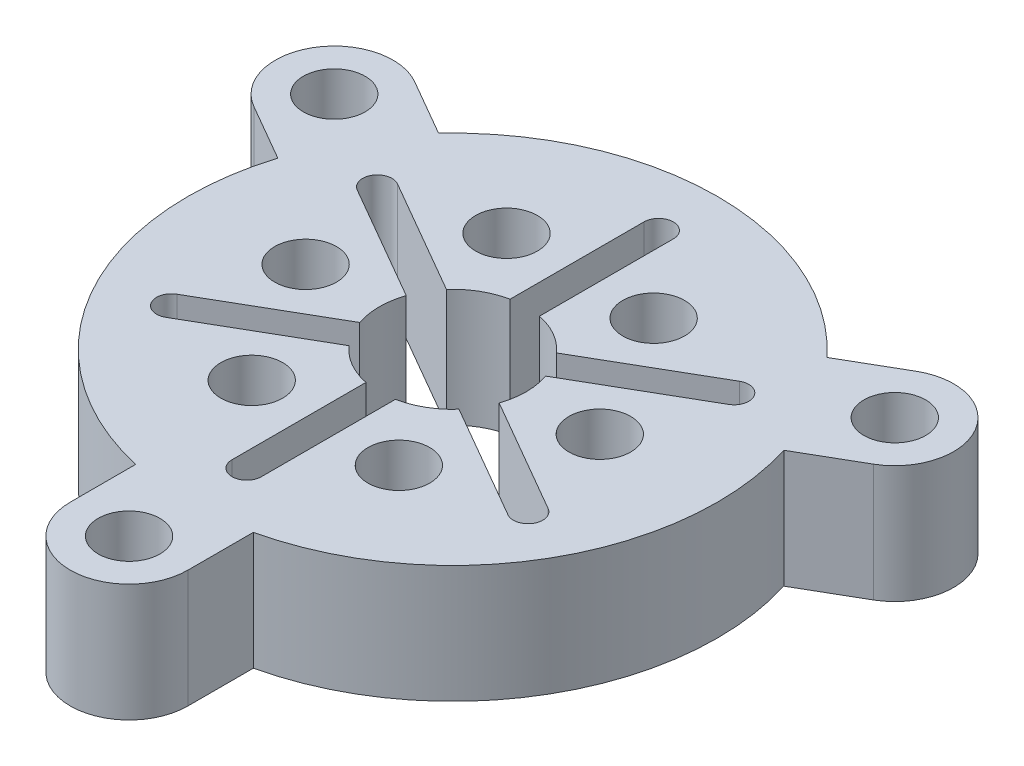
SolidWorks part; units mm, degrees
ref_plane "Front Plane" through (0, 0, 0) normal (0, 0, 1) x (1, 0, 0)
ref_plane "Top Plane" through (0, 0, 0) normal (0, 1, 0) x (1, 0, 0)
ref_plane "Right Plane" through (0, 0, 0) normal (1, 0, 0) x (0, 0, -1)
sketch "Sketch1" plane through (0, 0, 0) normal (0, 1, 0) x (1, 0, 0)
  line L0 (-4, -22) -> (-4, -17.5499)
  line L1 (4, -22) -> (4, -17.5499)
  line L2 (0, 0) -> (0, 14) construction
  line L3 (1, 4.899) -> (1, 14)
  line L4 (-1, 4.899) -> (-1, 14)
  line L5 (-21.0526, 7.5359) -> (-17.1987, 5.3109)
  line L6 (1, 0) -> (1, 14) construction
  line L7 (-1, 0) -> (-1, 14) construction
  line L8 (-17.0526, 14.4641) -> (-13.1987, 12.2391)
  line L9 (17.0526, 14.4641) -> (13.1987, 12.2391)
  line L10 (21.0526, 7.5359) -> (17.1987, 5.3109)
  line L11 (4.7426, 1.5835) -> (12.6244, 6.134)
  line L12 (3.7426, 3.3155) -> (11.6244, 7.866)
  line L13 (3.7426, -3.3155) -> (11.6244, -7.866)
  line L14 (4.7426, -1.5835) -> (12.6244, -6.134)
  line L15 (-1, -4.899) -> (-1, -14)
  line L16 (1, -4.899) -> (1, -14)
  line L17 (-4.7426, -1.5835) -> (-12.6244, -6.134)
  line L18 (-3.7426, -3.3155) -> (-11.6244, -7.866)
  line L19 (-3.7426, 3.3155) -> (-11.6244, 7.866)
  line L20 (-4.7426, 1.5835) -> (-12.6244, 6.134)
  arc A0 (-3.7426, -3.3155) -> (-1, -4.899) centre (0, 0) ccw
  arc A1 (4, -17.5499) -> (17.1987, 5.3109) centre (0, 0) ccw
  circle A2 centre (0, -22) radius 2.1
  arc A3 (-4, -22) -> (4, -22) centre (0, -22) ccw
  arc A5 (1, 14) -> (-1, 14) centre (0, 14) ccw
  arc A6 (-17.0526, 14.4641) -> (-21.0526, 7.5359) centre (-19.0526, 11) ccw
  circle A7 centre (-19.0526, 11) radius 2.1
  arc A8 (21.0526, 7.5359) -> (17.0526, 14.4641) centre (19.0526, 11) ccw
  circle A9 centre (19.0526, 11) radius 2.1
  arc A10 (12.6244, 6.134) -> (11.6244, 7.866) centre (12.1244, 7) ccw
  arc A11 (11.6244, -7.866) -> (12.6244, -6.134) centre (12.1244, -7) ccw
  arc A12 (-1, -14) -> (1, -14) centre (0, -14) ccw
  arc A13 (-12.6244, -6.134) -> (-11.6244, -7.866) centre (-12.1244, -7) ccw
  arc A14 (-11.6244, 7.866) -> (-12.6244, 6.134) centre (-12.1244, 7) ccw
  arc A15 (13.1987, 12.2391) -> (-13.1987, 12.2391) centre (0, 0) ccw
  arc A16 (-17.1987, 5.3109) -> (-4, -17.5499) centre (0, 0) ccw
  arc A17 (-4.7426, 1.5835) -> (-4.7426, -1.5835) centre (0, 0) ccw
  arc A18 (-1, 4.899) -> (-3.7426, 3.3155) centre (0, 0) ccw
  arc A19 (3.7426, 3.3155) -> (1, 4.899) centre (0, 0) ccw
  arc A20 (4.7426, -1.5835) -> (4.7426, 1.5835) centre (0, 0) ccw
  arc A21 (1, -4.899) -> (3.7426, -3.3155) centre (0, 0) ccw
  point P35 (0, 0)
  point P60 (0, 0)
  dimension "D1" = 10
  dimension "D2" = 36
  dimension "D3" = 4.2
  dimension "D5" = 8
  dimension "D4" = 22
  dimension "D6" = 14
  dimension "D7" = 1
  dimension "D8" = 1
  dimension "D9" = 3
  dimension "D10" = 6
extrude "Boss-Extrude1" add sketch "Sketch1" along normal blind 8
sketch "Sketch2" plane through (0, 8, 0) normal (0, 1, 0) x (1, 0, 0)
  circle A0 centre (10, 0) radius 2.1
  circle A1 centre (5, -8.6603) radius 2.1
  circle A2 centre (-5, -8.6603) radius 2.1
  circle A3 centre (-10, 0) radius 2.1
  circle A4 centre (-5, 8.6603) radius 2.1
  circle A5 centre (5, 8.6603) radius 2.1
  point P15 (0, 0)
  dimension "D2" = 4.2
  dimension "D1" = 10
  dimension "D3" = 6
extrude "Cut-Extrude1" cut sketch "Sketch2" against normal blind 5.8
